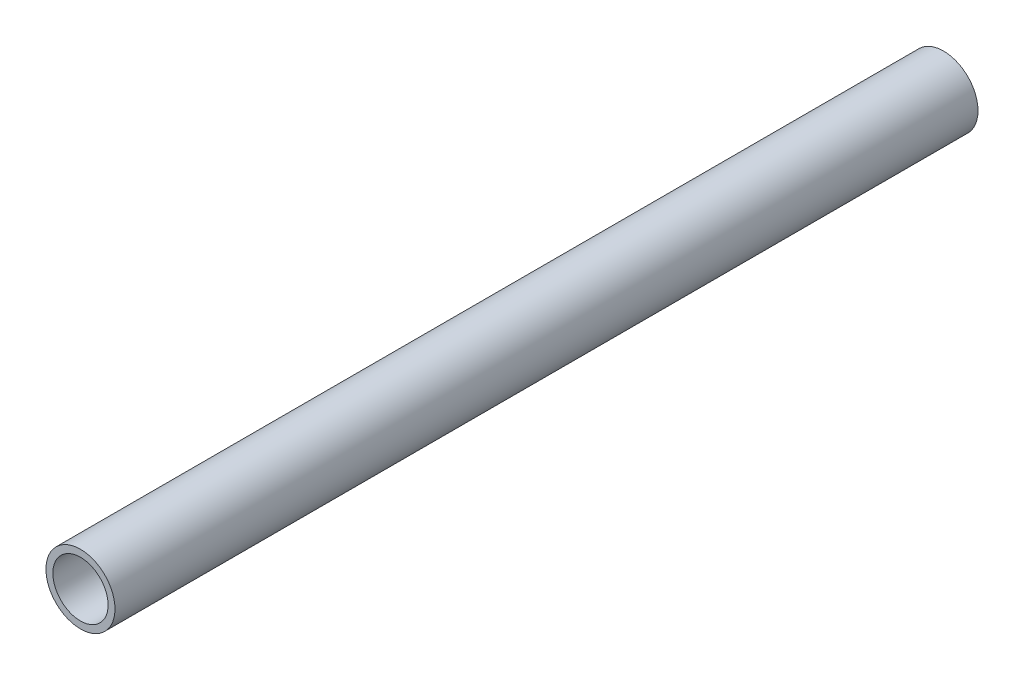
SolidWorks part; units mm, degrees
material "PVC Rigid"
ref_plane "Front Plane" through (0, 0, 0) normal (0, 0, 1) x (1, 0, 0)
ref_plane "Top Plane" through (0, 0, 0) normal (0, 1, 0) x (1, 0, 0)
ref_plane "Right Plane" through (0, 0, 0) normal (1, 0, 0) x (0, 0, -1)
sketch "Sketch1" plane through (0, 0, 0) normal (0, 0, 1) x (1, 0, 0)
  circle A0 centre (0, 0) radius 12.7
  circle A1 centre (0, 0) radius 10.16
  dimension "D1" = 25.4
  dimension "D2" = 20.32
extrude "Boss-Extrude1" add sketch "Sketch1" along normal blind 317.5
